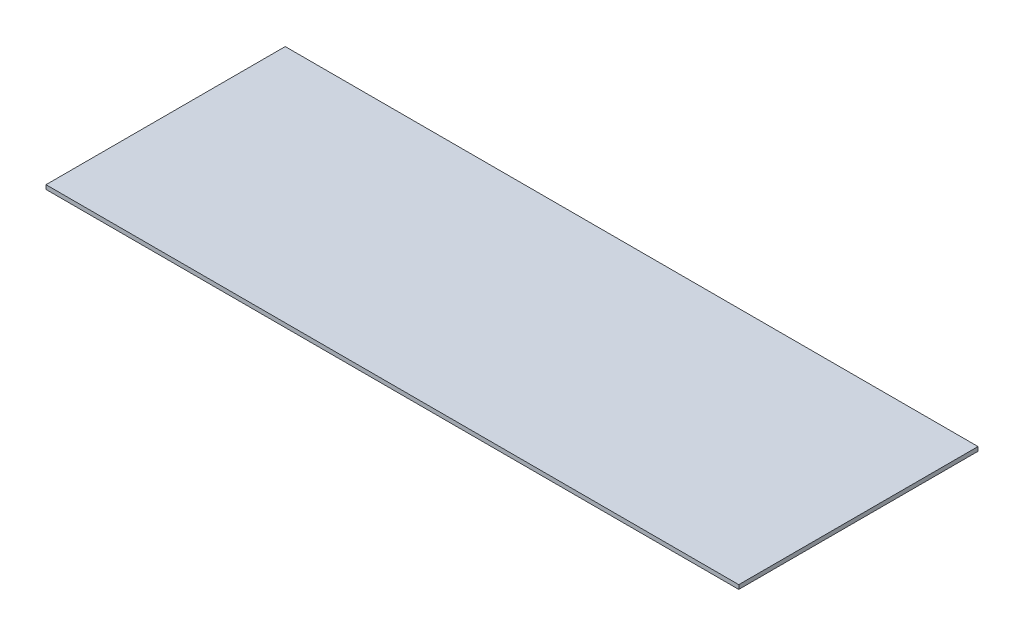
SolidWorks part; units mm, degrees
ref_plane "前视基准面" through (0, 0, 0) normal (0, 0, 1) x (1, 0, 0)
ref_plane "上视基准面" through (0, 0, 0) normal (0, 1, 0) x (1, 0, 0)
ref_plane "右视基准面" through (0, 0, 0) normal (1, 0, 0) x (0, 0, -1)
sketch "草图1" plane through (0, 0, 0) normal (0, 1, 0) x (1, 0, 0)
  line L1 (0, 0) -> (300, 0)
  line L2 (0, 0) -> (0, 103.6)
  line L3 (0, 103.6) -> (300, 103.6)
  line L4 (300, 0) -> (300, 103.6)
  dimension "D1" = 300
  dimension "D2" = 103.6
extrude "凸台-拉伸1" add sketch "草图1" along normal blind 1.8
